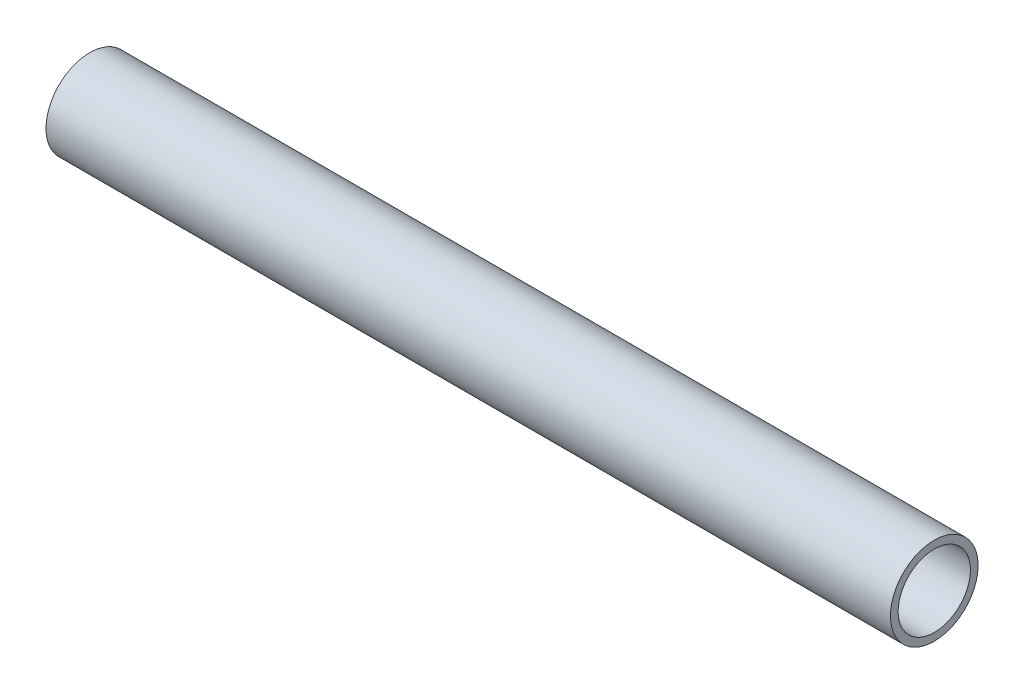
SolidWorks part; units mm, degrees
ref_plane "Front Plane" through (0, 0, 0) normal (0, 0, 1) x (1, 0, 0)
ref_plane "Top Plane" through (0, 0, 0) normal (0, 1, 0) x (1, 0, 0)
ref_plane "Right Plane" through (0, 0, 0) normal (1, 0, 0) x (0, 0, -1)
sketch "Sketch1" plane through (0, 0, 0) normal (0, 0, 1) x (1, 0, 0)
  line L0 (0, 24.264) -> (0, -25.166) construction
  line L1 (-17.1381, 0) -> (52.136, 0) construction
  line L3 (0, 21.082) -> (406.4, 21.082)
  line L4 (0, 21.082) -> (0, 17.399)
  line L5 (0, 17.399) -> (406.4, 17.399)
  line L6 (406.4, 21.082) -> (406.4, 17.399)
  dimension "D1" = 34.798
  dimension "D2" = 42.164
  dimension "D3" = 406.4
revolve "Revolve1" add sketch "Sketch1" angle 360 about L1
